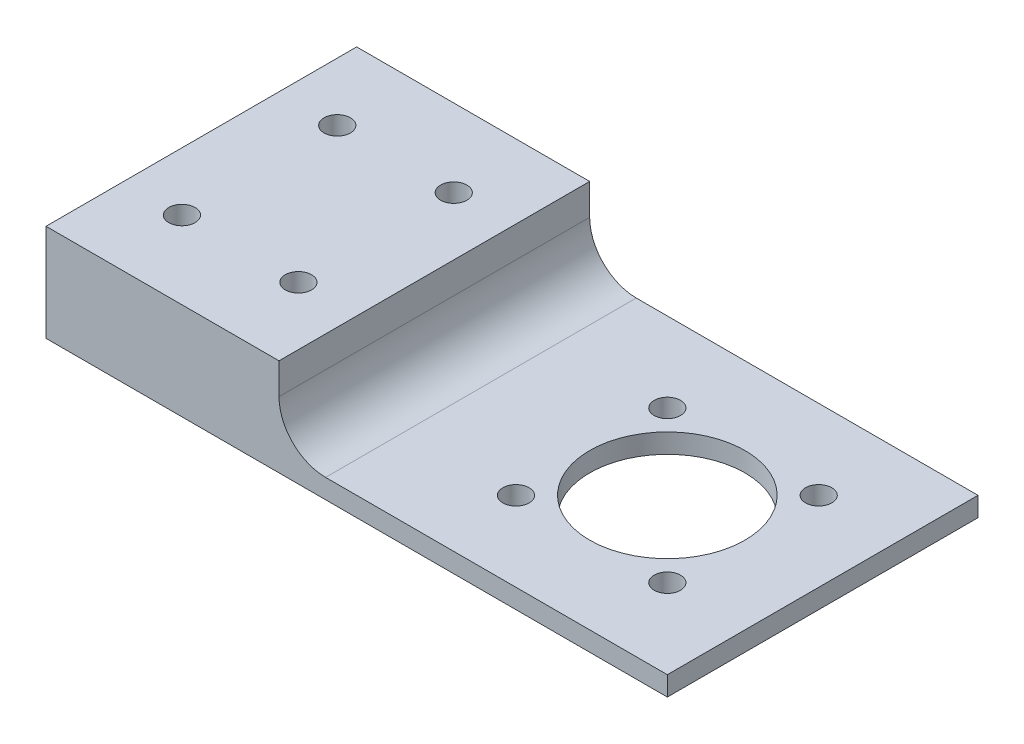
SolidWorks part; units mm, degrees
material "6061-T6 (SS)"
ref_plane "Front Plane" through (0, 0, 0) normal (0, 0, 1) x (1, 0, 0)
ref_plane "Top Plane" through (0, 0, 0) normal (0, 1, 0) x (1, 0, 0)
ref_plane "Right Plane" through (0, 0, 0) normal (1, 0, 0) x (0, 0, -1)
sketch "Sketch1" plane through (0, 0, 0) normal (0, 1, 0) x (1, 0, 0)
  line L2 (50.8, 25.4) -> (63.5, 25.4)
  line L3 (63.5, 25.4) -> (63.5, -25.4)
  line L4 (0, 0) -> (-47.453, 0) construction
  line L7 (63.5, -25.4) -> (50.8, -25.4)
  line L8 (50.8, 25.4) -> (0, 25.4)
  line L9 (0, 25.4) -> (0, -25.4) construction
  line L10 (0, -25.4) -> (50.8, -25.4)
  line L11 (-38.1, 25.4) -> (-38.1, -25.4)
  line L12 (-38.1, 25.4) -> (0, 25.4)
  line L13 (-38.1, -25.4) -> (0, -25.4)
  circle A0 centre (38.1, 0) radius 6.35 construction
  circle A1 centre (38.1, 0) radius 17.5 construction
  point P1 (0, 0)
  point P9 (44.45, 0)
  point P22 (63.5, 0)
  dimension "D1" = 19.05
  dimension "D3" = 38.1
  dimension "D2" = 12.7
  dimension "D4" = 35
  dimension "D5" = 50.8
  dimension "D6" = 38.1
extrude "Boss-Extrude1" add sketch "Sketch1" along normal blind 3.175
sketch "Sketch6" plane through (0, 3.175, 0) normal (0, 1, 0) x (1, 0, 0)
  line L0 (-38.1, 25.4) -> (-38.1, -25.4) construction
  line L1 (-38.1, 25.4) -> (0, 25.4)
  line L2 (-38.1, 25.4) -> (-38.1, -25.4)
  line L3 (-38.1, -25.4) -> (0, -25.4)
  line L4 (0, 25.4) -> (0, -25.4)
  line L5 (-38.1, -25.4) -> (63.5, -25.4) construction
  dimension "D1" = 38.1
  dimension "D2" = 50.8
extrude "Boss-Extrude3" add sketch "Sketch6" along normal blind 12.7
fillet "Fillet1" radius 7.62 1 edges at (0, 3.175, 0)
sketch "Sketch2" plane through (0, 3.175, 0) normal (0, 1, 0) x (1, 0, 0)
  line L0 (38.1, 0) -> (73.074, 0) construction
  line L1 (5.6791, -32.4209) -> (70.5209, 32.4209) construction
  line L2 (3.126, 34.974) -> (73.074, -34.974) construction
  circle A2 centre (38.1, 0) radius 17.5 construction
  circle A3 centre (50.4744, 12.3744) radius 2.1527
  circle A7 centre (50.4744, -12.3744) radius 2.1527
  circle A8 centre (25.7256, -12.3744) radius 2.1527
  circle A9 centre (25.7256, 12.3744) radius 2.1527
  circle A10 centre (38.1, 0) radius 5.2921 construction
  point P1 (0, 0)
  point P4 (50.4744, 12.3744)
  point P6 (25.7256, -12.3744)
  point P21 (38.1, 0)
  point P24 (38.1, 0)
  dimension "D1" = 35
  dimension "D2" = 4.3053
  dimension "D8" = 10.5841
  dimension "D3" = 45
  dimension "D4" = 45
  dimension "D5" = 38.1
  dimension "D6" = 12.3744
  dimension "D7" = 25.7256
extrude "MountingHolesM4" cut sketch "Sketch2" against normal up to surface (3.175 mm away) up to face at (12.7, 0, 0)
sketch "Sketch5" plane through (0, 3.175, 0) normal (0, 1, 0) x (1, 0, 0)
  circle A0 centre (38.1, 0) radius 12.7
  dimension "D1" = 25.4
  dimension "D2" = 38.1
extrude "HoleFor25mmOutCropping" cut sketch "Sketch5" against normal up to surface (3.175 mm away) up to face at (50.4744, 0, -14.527)
sketch "Sketch7" plane through (0, 0, 0) normal (0, -1, 0) x (1, 0, 0)
  line L0 (0, 0) -> (-53.2461, 0) construction
  circle A0 centre (-9.525, -12.7) radius 2.1526
  circle A1 centre (-28.575, -12.7) radius 2.1527
  circle A10 centre (-9.525, 12.7) radius 2.1526
  circle A12 centre (-28.575, 12.7) radius 2.1527
  dimension "D4" = 4.3053
  dimension "D1" = 9.525
  dimension "D2" = 12.7
  dimension "D3" = 19.05
extrude "Cut-Extrude4" cut sketch "Sketch7" against normal up to surface (15.875 mm away) up to face at (-19.05, 15.875, 0)
sketch "Sketch8" [suppressed] plane through (0, 0, 0) normal (0, -1, 0) x (1, 0, 0)
  circle A2 centre (38.1, 0) radius 15.875
  dimension "D1" = 31.75
  dimension "D2" = 38.1
extrude "ThruHoleFor1.180\"BearingOD" [suppressed] cut sketch "Sketch8" against normal up to next
sketch "Sketch9" [suppressed] plane through (0, 0, 0) normal (0, -1, 0) x (1, 0, 0)
  line L0 (2.3424, 35.7576) -> (73.8576, -35.7576) construction
  line L1 (38.1, 0) -> (38.1, -76.7065) construction
  circle A0 centre (38.1, 0) radius 20.193 construction
  circle A1 centre (52.3786, -14.2786) radius 1.7272
  circle A2 centre (23.8214, 14.2786) radius 1.7272
  point P10 (38.1, 0)
  dimension "D2" = 40.386
  dimension "D3" = 3.4544
  dimension "D1" = 38.1
  dimension "D4" = 45
extrude "TappedHoleFor8-32,BoltMustBe.375\"Long" [suppressed] cut sketch "Sketch9" against normal up to next
sketch "Sketch10" plane through (0, 3.175, 0) normal (0, 1, 0) x (1, 0, 0)
  circle A0 centre (38.1, 0) radius 12.7 construction
  circle A1 centre (38.1, 0) radius 12.7
